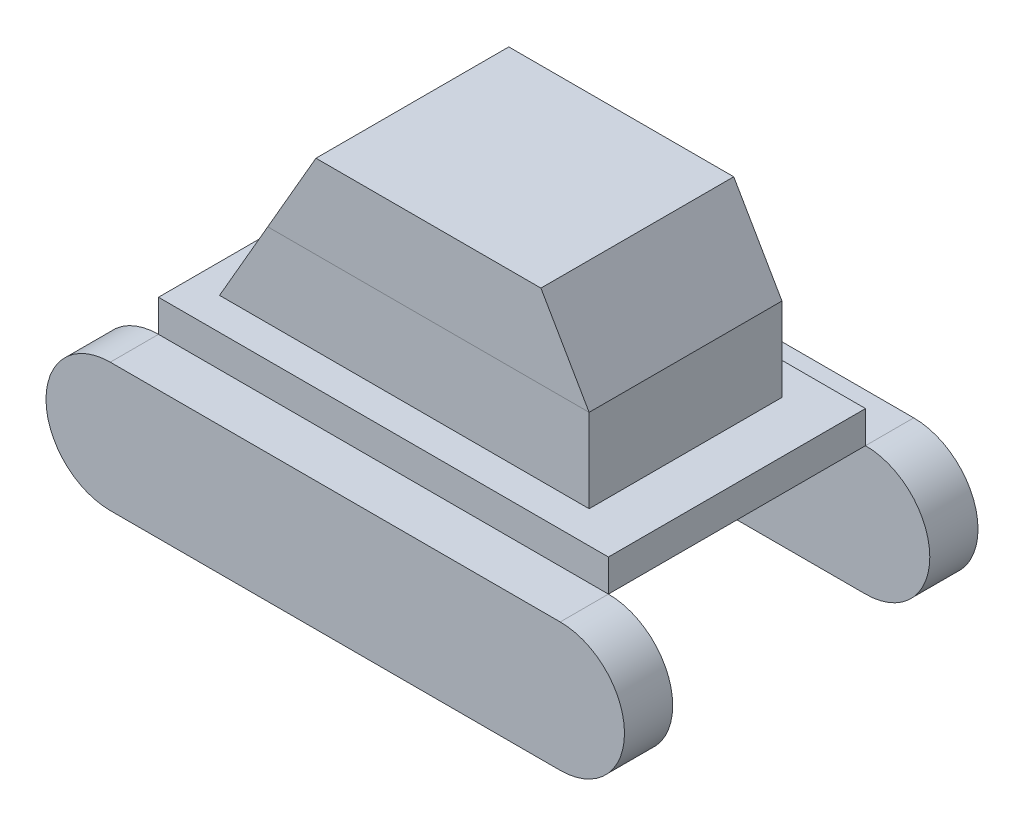
SolidWorks part; units mm, degrees
ref_plane "Front Plane" through (0, 0, 0) normal (0, 0, 1) x (1, 0, 0)
ref_plane "Top Plane" through (0, 0, 0) normal (0, 1, 0) x (1, 0, 0)
ref_plane "Right Plane" through (0, 0, 0) normal (1, 0, 0) x (0, 0, -1)
sketch "Sketch1" plane through (0, 0, 0) normal (0, 0, 1) x (1, 0, 0)
  line L0 (0, 40) -> (140, 40)
  line L1 (0, 0) -> (140, 0)
  arc A0 (0, 40) -> (0, 0) centre (0, 20) ccw
  arc A1 (140, 0) -> (140, 40) centre (140, 20) ccw
  dimension "D1" = 40
  dimension "D3" = 140
extrude "Boss-Extrude1" add sketch "Sketch1" along normal blind 15
ref_plane "Plane2" through (0, 40, 0) normal (0, 1, 0) x (1, 0, 0)
sketch "Sketch2" plane through (0, 40, 0) normal (0, 1, 0) x (1, 0, 0)
  line L1 (0, -15) -> (140, -15)
  line L2 (0, -15) -> (0, -95)
  line L3 (0, -95) -> (140, -95)
  line L4 (140, -15) -> (140, -95)
  dimension "D1" = 80
  dimension "D2" = 140
extrude "Boss-Extrude2" add sketch "Sketch2" along normal blind 10 separate body
ref_plane "Plane3" through (0, 0, 25) normal (0, 0, -1) x (-1, 0, 0)
sketch "Sketch3" plane through (0, 0, 25) normal (0, 0, -1) x (-1, 0, 0)
  line L0 (-9, 50) -> (-39, 101.9615)
  line L1 (-140, 50) -> (0, 50) construction
  line L2 (-39, 101.9615) -> (-109, 101.9615)
  line L3 (-109, 101.9615) -> (-124, 75.9808)
  line L4 (-124, 75.9808) -> (-124, 50)
  line L5 (-124, 50) -> (-9, 50)
  line L6 (0, 50) -> (0, 40) construction
  point P9 (0, 50)
  dimension "D1" = 60
  dimension "D2" = 70
  dimension "D3" = 60
  dimension "D4" = 9
  dimension "D5" = 30
  dimension "D6" = 120
extrude "Boss-Extrude3" add sketch "Sketch3" against normal blind 60
sketch "Sketch4" plane through (0, 0, 95) normal (0, 0, 1) x (1, 0, 0)
  line L0 (0, 40) -> (140, 40)
  line L1 (0, 0) -> (140, 0)
  arc A0 (0, 40) -> (0, 0) centre (0, 20) ccw
  arc A1 (140, 0) -> (140, 40) centre (140, 20) ccw
extrude "Boss-Extrude4" add sketch "Sketch4" along normal blind 15 separate body
sketch "Sketch5" plane through (0, 0, 85) normal (0, 0, 1) x (1, 0, 0)
  line L0 (124, 75.9808) -> (24, 75.9808)
  line L1 (9, 50) -> (39, 101.9615) construction
split line "Split Line1"
sketch "Sketch6" plane through (0, 0, 25) normal (0, 0, -1) x (-1, 0, 0)
  line L0 (-124, 75.9808) -> (-24, 75.9808)
  line L1 (-9, 50) -> (-39, 101.9615) construction
split line "Split Line2"
sketch "Sketch7" plane through (-14.9006, 8.6029, 0) normal (-0.866, 0.5, 0) x (0, 0, 1)
  line L0 (25, 77.8013) -> (85, 77.8013)
  line L1 (85, 47.8013) -> (85, 77.8013) construction
split line "Split Line3"
sketch "Sketch8" plane through (-14.9006, 8.6029, 0) normal (-0.866, 0.5, 0) x (0, 0, 1)
  line L0 (55, 107.8013) -> (55, 77.8013)
  line L1 (85, 107.8013) -> (25, 107.8013) construction
  line L2 (85, 77.8013) -> (25, 77.8013) construction
split line "Split Line4"
